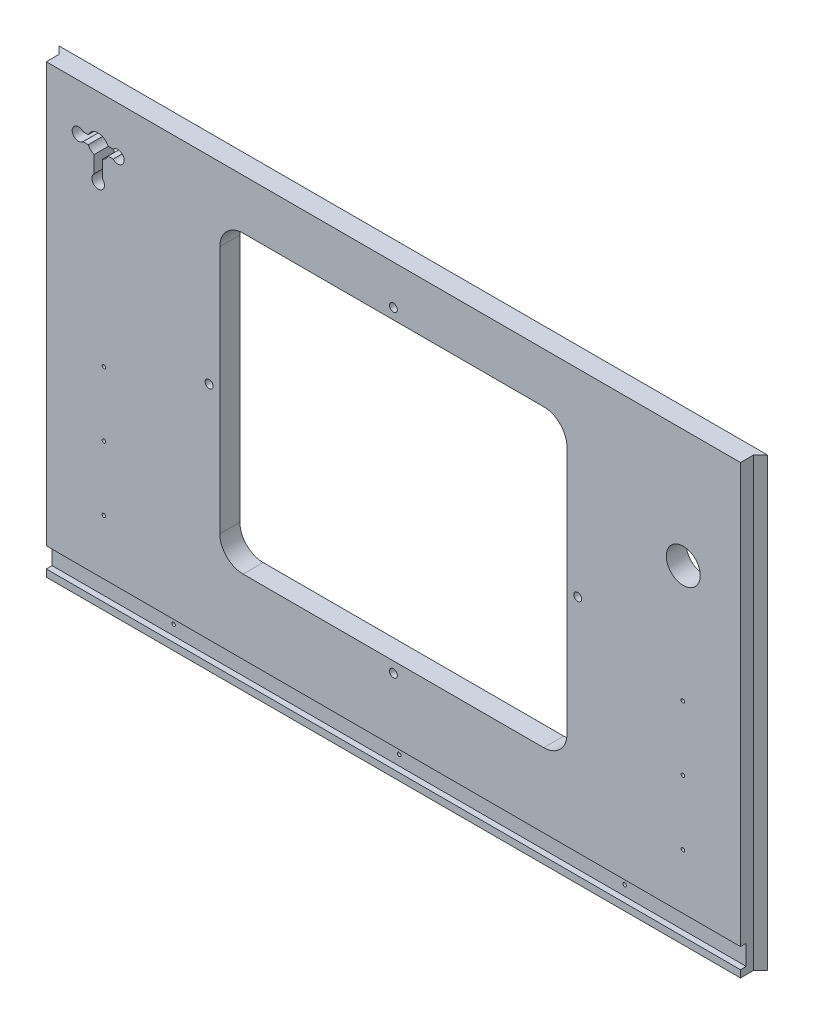
SolidWorks part; units mm, degrees
material "Pine"
ref_plane "Front Plane" through (0, 0, 0) normal (0, 0, 1) x (1, 0, 0)
ref_plane "Top Plane" through (0, 0, 0) normal (0, 1, 0) x (1, 0, 0)
ref_plane "Right Plane" through (0, 0, 0) normal (1, 0, 0) x (0, 0, -1)
sketch "Sketch1" plane through (0, 0, 0) normal (0, 0, 1) x (1, 0, 0)
  line L0 (8932.6508, -5243.5125) -> (10226.1458, -5243.5125)
  line L1 (9086.3208, -4722.0918) -> (10222.9708, -4853.7812)
  line L2 (8914.8708, -6342.0625) -> (10197.5708, -6342.0625)
  line L3 (8914.8708, -5808.6625) -> (10197.5708, -5808.6625)
  line L4 (8919.6333, -5253.0375) -> (10218.2083, -5253.0375)
  line L5 (9134.2633, -4656.1375) -> (9134.2633, -4638.3575)
  line L6 (9091.0833, -4638.3575) -> (9134.2633, -4638.3575)
  line L7 (9091.0833, -4567.2375) -> (9091.0833, -4638.3575)
  line L8 (9134.2633, -4656.1375) -> (9581.3033, -4656.1375)
  line L9 (9091.0833, -4567.2375) -> (9624.4833, -4567.2375)
  line L10 (9581.3033, -4656.1375) -> (9581.3033, -4638.3575)
  line L11 (9581.3033, -4638.3575) -> (9624.4833, -4638.3575)
  line L12 (9624.4833, -4567.2375) -> (9624.4833, -4638.3575)
  line L13 (8932.6508, -5225.7325) -> (9344.9775, -5225.7325)
  line L14 (8932.6508, -5256.2125) -> (8932.6508, -5243.5125)
  line L15 (8911.6958, -5256.2125) -> (8932.6508, -5256.2125)
  line L16 (8914.8708, -4722.0918) -> (9086.3208, -4722.0918)
  line L17 (8911.6958, -4715.5913) -> (8932.6508, -4715.5913)
  line L18 (8914.8708, -6342.0625) -> (8914.8708, -5808.6625)
  line L19 (12082.9917, -4722.0918) -> (10946.3417, -4853.7812)
  line L20 (12236.6617, -5243.5125) -> (10943.1667, -5243.5125)
  line L21 (10951.1042, -5253.0375) -> (12249.6792, -5253.0375)
  line L22 (10838.3917, -5656.2625) -> (11308.2917, -5656.2625)
  line L23 (10838.3917, -5719.7625) -> (11308.2917, -5719.7625)
  line L24 (10838.3917, -5742.5368) -> (11308.2917, -5742.5368)
  line L25 (10806.6417, -6342.0625) -> (11340.0417, -6342.0625)
  line L26 (10803.4667, -6335.7125) -> (11343.2167, -6335.7125)
  line L27 (10803.4667, -6317.9325) -> (11343.2167, -6317.9325)
  line L28 (10943.1667, -5225.7325) -> (11376.4483, -5225.7325)
  line L29 (11506.7292, -4754.5625) -> (10806.6417, -4827.5875)
  line L30 (11506.7292, -4567.2375) -> (11506.7292, -4754.5625)
  line L31 (10806.6417, -4567.2375) -> (10806.6417, -4827.5875)
  line L32 (10806.6417, -4567.2375) -> (11506.7292, -4567.2375)
  line L33 (10235.6708, -6329.3625) -> (10245.1958, -6329.3625)
  line L34 (10245.1958, -6329.3625) -> (10254.7208, -6278.5625)
  line L35 (10302.3458, -6329.3625) -> (10311.8708, -6278.5625)
  line L36 (10302.3458, -6329.3625) -> (10292.8208, -6329.3625)
  line L37 (10245.1958, -5821.3625) -> (10254.7208, -5872.1625)
  line L38 (10235.6708, -5821.3625) -> (10245.1958, -5821.3625)
  line L39 (10292.8208, -5821.3625) -> (10302.3458, -5821.3625)
  line L40 (10302.3458, -5821.3625) -> (10311.8708, -5872.1625)
  line L41 (10235.6708, -5821.3625) -> (10235.6708, -6329.3625)
  line L42 (10254.7208, -5872.1625) -> (10254.7208, -6278.5625)
  line L43 (10311.8708, -5872.1625) -> (10311.8708, -6278.5625)
  line L44 (10292.8208, -5821.3625) -> (10292.8208, -6329.3625)
  line L45 (8932.6508, -5225.7325) -> (8932.6508, -4715.5913)
  line L46 (8911.6958, -4715.5913) -> (8911.6958, -5256.2125)
  line L47 (8914.8708, -5248.275) -> (8914.8708, -4722.0918)
  line L48 (8919.6333, -5253.0375) -> (8914.8708, -5248.275)
  line L49 (8914.8708, -5145.0875) -> (8937.426, -5145.0875)
  line L50 (8914.8708, -5202.2375) -> (8937.426, -5202.2375)
  line L51 (10838.3917, -5656.2625) -> (10838.3917, -5719.7625)
  line L52 (10832.0417, -5736.1868) -> (10856.1717, -5736.1868)
  line L53 (10806.6417, -6342.0625) -> (10806.6417, -5818.7368)
  line L54 (10832.0417, -5649.9125) -> (10856.1717, -5649.9125)
  line L55 (10832.0417, -5726.1125) -> (10856.1717, -5726.1125)
  line L56 (10806.6417, -5818.7368) -> (10833.9015, -5818.7368)
  line L57 (10832.0417, -5806.0442) -> (10851.6815, -5806.0442)
  line L58 (10856.1717, -5801.5541) -> (10856.1717, -5736.1868)
  line L59 (10838.3917, -5814.2467) -> (10838.3917, -5742.5368)
  line L60 (10832.0417, -5806.0442) -> (10832.0417, -5736.1868)
  line L61 (10803.4667, -6317.9325) -> (10803.4667, -6335.7125)
  line L62 (10197.5708, -5808.6625) -> (10197.5708, -6342.0625)
  line L63 (9762.3842, -6348.4125) -> (9762.3842, -5802.3125)
  line L64 (9780.1642, -6348.4125) -> (9762.3842, -6348.4125)
  line L65 (9780.1642, -5802.3125) -> (9780.1642, -6348.4125)
  line L66 (9762.3842, -5802.3125) -> (9780.1642, -5802.3125)
  line L67 (9332.2775, -6348.4125) -> (9332.2775, -5802.3125)
  line L68 (9332.2775, -6348.4125) -> (9350.0575, -6348.4125)
  line L69 (9350.0575, -5802.3125) -> (9350.0575, -6348.4125)
  line L70 (9332.2775, -5802.3125) -> (9350.0575, -5802.3125)
  line L71 (9993.8374, -6061.075) -> (9993.8374, -6045.2418)
  line L72 (9998.5999, -6065.8375) -> (10014.4331, -6065.8375)
  line L73 (9998.5999, -6084.8875) -> (10014.4331, -6084.8875)
  line L74 (9993.8374, -6105.4832) -> (9993.8374, -6089.65)
  line L75 (9974.7874, -6105.4832) -> (9974.7874, -6089.65)
  line L76 (9954.1917, -6084.8875) -> (9970.0249, -6084.8875)
  line L77 (9974.7874, -6061.075) -> (9974.7874, -6045.2418)
  line L78 (9954.1917, -6065.8375) -> (9970.0249, -6065.8375)
  line L79 (10793.9417, -6237.2875) -> (10816.4969, -6237.2875)
  line L80 (10793.9417, -6294.4375) -> (10816.4969, -6294.4375)
  line L81 (10856.1717, -5649.9125) -> (10856.1717, -5726.1125)
  line L82 (10832.0417, -5726.1125) -> (10832.0417, -5649.9125)
  line L83 (10226.1458, -5225.7325) -> (10226.1458, -5243.5125)
  line L84 (10205.1908, -5257.8) -> (10205.1908, -4844.2499)
  line L85 (10230.9083, -4844.2499) -> (10230.9083, -5257.8)
  line L86 (10205.1908, -5257.8) -> (10230.9083, -5257.8)
  line L87 (10205.1908, -4844.2499) -> (10230.9083, -4844.2499)
  line L88 (10946.3417, -5176.8375) -> (10968.8969, -5176.8375)
  line L89 (9349.4676, -5141.9125) -> (9358.2674, -5141.9125)
  line L90 (10946.3417, -5119.6875) -> (10968.8969, -5119.6875)
  line L91 (9929.011, -4660.9635) -> (10066.0807, -4660.9635)
  line L92 (9929.011, -4678.7435) -> (10066.0807, -4678.7435)
  line L93 (10943.1667, -5225.7325) -> (10943.1667, -5243.5125)
  line L94 (10946.3417, -5248.275) -> (10951.1042, -5253.0375)
  line L95 (10946.3417, -5257.8063) -> (10946.3417, -4849.0188)
  line L96 (10964.1217, -5257.8) -> (10964.1217, -4844.2499)
  line L97 (10938.4042, -4844.2499) -> (10938.4042, -5257.8)
  line L98 (10938.4042, -5257.8) -> (10964.1217, -5257.8)
  line L99 (10964.1217, -4844.2499) -> (10938.4042, -4844.2499)
  line L100 (10344.8908, -4560.8875) -> (10369.0208, -4560.8875)
  line L101 (10344.8908, -4560.8875) -> (10369.0208, -4560.8875)
  line L102 (10800.2917, -4560.8875) -> (10824.4217, -4560.8875)
  line L103 (10200.4156, -5119.6875) -> (10222.9708, -5119.6875)
  line L104 (10200.4156, -5176.8375) -> (10222.9708, -5176.8375)
  line L105 (9344.9775, -5146.4026) -> (9344.9775, -5225.7325)
  line L106 (10344.8908, -4560.8875) -> (10344.8908, -4833.9375)
  line L107 (9792.8642, -5225.7325) -> (9792.8642, -5146.4026)
  line L108 (9362.7575, -5225.7325) -> (9775.0842, -5225.7325)
  line L109 (9680.3633, -4761.8396) -> (9680.3633, -4559.9604)
  line L110 (9656.2333, -4559.9604) -> (9680.3633, -4559.9604)
  line L111 (9656.2333, -4761.8396) -> (9680.3633, -4761.8396)
  line L112 (9656.2333, -4761.8396) -> (9656.2333, -4559.9604)
  line L113 (9779.5743, -5141.9125) -> (9788.374, -5141.9125)
  line L114 (10070.5708, -4665.4536) -> (10070.5708, -4674.2534)
  line L115 (9924.5208, -4674.2534) -> (9924.5208, -4665.4536)
  line L116 (12127.4417, -6188.3925) -> (12205.5015, -6188.3925)
  line L117 (12209.9917, -6170.6125) -> (12209.9917, -6183.9024)
  line L118 (9792.8642, -5225.7325) -> (10226.1458, -5225.7325)
  line L119 (9662.5833, -4754.5625) -> (10362.6708, -4827.5875)
  line L120 (9662.5833, -4567.2375) -> (9662.5833, -4754.5625)
  line L121 (10362.6708, -4567.2375) -> (10362.6708, -4827.5875)
  line L122 (9662.5833, -4567.2375) -> (10362.6708, -4567.2375)
  line L123 (10824.4217, -4833.9375) -> (10800.2917, -4833.9375)
  line L124 (10800.2917, -4833.9375) -> (10800.2917, -4560.8875)
  line L125 (10824.4217, -4560.8875) -> (10824.4217, -4833.9375)
  line L126 (10344.8908, -4833.9375) -> (10369.0208, -4833.9375)
  line L127 (10369.0208, -4833.9375) -> (10369.0208, -4560.8875)
  line L128 (10222.9708, -5248.275) -> (10218.2083, -5253.0375)
  line L129 (10222.9708, -5257.8063) -> (10222.9708, -4849.0188)
  line L130 (11734.6544, -5701.375) -> (11739.2301, -5701.375)
  line L131 (9362.7575, -5225.7325) -> (9362.7575, -5146.4026)
  line L132 (9775.0842, -5146.4026) -> (9775.0842, -5225.7325)
  line L133 (11761.3864, -5701.375) -> (11756.8282, -5701.375)
  line L134 (11734.6544, -5693.755) -> (11739.2301, -5693.755)
  line L135 (11761.4039, -5693.755) -> (11756.8282, -5693.755)
  line L136 (11734.6544, -5701.375) -> (11739.2301, -5701.375)
  line L137 (11744.3462, -5721.3024) -> (11744.3462, -5706.4179)
  line L138 (11751.7122, -5721.3024) -> (11751.7122, -5706.4179)
  line L139 (11740.0917, -6170.6125) -> (11740.0917, -6183.9024)
  line L140 (11689.2917, -6188.3925) -> (11822.6417, -6188.3925)
  line L141 (11689.2917, -6348.4093) -> (11689.2917, -6164.2657)
  line L142 (11689.2917, -6164.2657) -> (11746.4417, -6164.2657)
  line L143 (11746.4417, -6164.2657) -> (11746.4417, -6188.3925)
  line L144 (11689.2917, -6164.2657) -> (11746.4417, -6164.2657)
  line L145 (11340.0417, -5818.7368) -> (11340.0417, -6342.0625)
  line L146 (11290.5117, -5726.1125) -> (11314.6417, -5726.1125)
  line L147 (11290.5117, -5649.9125) -> (11290.5117, -5726.1125)
  line L148 (11340.0417, -5818.7368) -> (11312.7818, -5818.7368)
  line L149 (11314.6417, -5806.0442) -> (11295.0018, -5806.0442)
  line L150 (11290.5117, -5801.5541) -> (11290.5117, -5736.1868)
  line L151 (11308.2917, -5814.2467) -> (11308.2917, -5742.5368)
  line L152 (11314.6417, -5806.0442) -> (11314.6417, -5736.1868)
  line L153 (11290.5117, -5736.1868) -> (11314.6417, -5736.1868)
  line L154 (11848.0417, -6267.1325) -> (11962.3417, -6267.1325)
  line L155 (11962.3417, -6267.1325) -> (11962.3417, -6203.6325)
  line L156 (11343.2167, -6317.9325) -> (11343.2167, -6335.7125)
  line L157 (11365.4417, -5656.2625) -> (11365.4417, -5719.7625)
  line L158 (11365.4417, -5656.2625) -> (11479.7417, -5656.2625)
  line L159 (11778.1917, -6071.3937) -> (11802.3217, -6071.3937)
  line L160 (11314.6417, -5726.1125) -> (11314.6417, -5649.9125)
  line L161 (11314.6417, -5649.9125) -> (11290.5117, -5649.9125)
  line L162 (11308.2917, -5719.7625) -> (11308.2917, -5656.2625)
  line L163 (11689.2917, -6348.4093) -> (11713.4217, -6348.4093)
  line L164 (12203.6417, -6164.2657) -> (12260.7917, -6164.2657)
  line L165 (11713.4217, -6348.4093) -> (11713.4217, -6164.2657)
  line L166 (11695.6417, -6342.0625) -> (11695.6417, -6170.6125)
  line L167 (11695.6417, -6048.5337) -> (11699.4517, -6052.3437)
  line L168 (11822.6417, -6292.5325) -> (11822.6417, -6188.3925)
  line L169 (11695.6417, -6342.0625) -> (11695.6417, -6170.6125)
  line L170 (11848.0417, -6203.6325) -> (11962.3417, -6203.6325)
  line L171 (11848.0417, -6203.6325) -> (11848.0417, -6267.1325)
  line L172 (11987.7417, -6267.1325) -> (11987.7417, -6203.6325)
  line L173 (11784.5417, -6077.7437) -> (11784.5417, -6141.2438)
  line L174 (11517.8417, -5656.2625) -> (11632.1417, -5656.2625)
  line L175 (11632.1417, -5656.2625) -> (11632.1417, -5719.7625)
  line L176 (11632.1417, -5719.7625) -> (11517.8417, -5719.7625)
  line L177 (11517.8417, -5719.7625) -> (11517.8417, -5656.2625)
  line L178 (11692.4667, -6028.2137) -> (11692.4667, -6045.9937)
  line L179 (11695.6417, -5979.3188) -> (11718.1969, -5979.3188)
  line L180 (11695.6417, -5922.1687) -> (11718.1969, -5922.1687)
  line L181 (11821.0415, -5722.9375) -> (11821.0415, -5943.6)
  line L182 (11687.7042, -5651.5) -> (11701.9917, -5651.5)
  line L183 (11687.7042, -5651.5) -> (11687.7042, -6055.5251)
  line L184 (11687.7042, -6055.5251) -> (11701.9917, -6055.5251)
  line L185 (11701.9917, -6055.5251) -> (11701.9917, -5651.5)
  line L186 (11695.6417, -6055.2013) -> (11695.6417, -5649.595)
  line L187 (11695.6417, -5656.2625) -> (11695.6417, -6048.5337)
  line L188 (11695.6417, -6170.6125) -> (11740.0917, -6170.6125)
  line L189 (12203.6417, -6164.2657) -> (12203.6417, -6188.3925)
  line L190 (12254.4417, -6342.0625) -> (12254.4417, -6170.6125)
  line L191 (12129.0419, -5943.6) -> (12129.0419, -5722.9375)
  line L192 (12254.4417, -6048.5337) -> (12250.6317, -6052.3437)
  line L193 (12257.6167, -6045.9937) -> (12257.6167, -6028.2137)
  line L194 (12248.0917, -5651.5) -> (12262.3792, -5651.5)
  line L195 (12262.3792, -5651.5) -> (12262.3792, -6055.5251)
  line L196 (12262.3792, -6055.5251) -> (12248.0917, -6055.5251)
  line L197 (12248.0917, -6055.5251) -> (12248.0917, -5651.5)
  line L198 (12254.4417, -6141.2438) -> (12254.4417, -6077.7437)
  line L199 (12236.6617, -6164.2657) -> (12260.7917, -6164.2657)
  line L200 (12102.0417, -6267.1325) -> (11987.7417, -6267.1325)
  line L201 (11330.1865, -6237.2875) -> (11352.7417, -6237.2875)
  line L202 (11330.1865, -6294.4375) -> (11352.7417, -6294.4375)
  line L203 (11474.6617, -5851.8425) -> (11492.4417, -5851.8425)
  line L204 (11474.6617, -5808.6625) -> (11474.6617, -5851.8425)
  line L205 (11403.5417, -5808.6625) -> (11474.6617, -5808.6625)
  line L206 (11492.4417, -5851.8425) -> (11492.4417, -6298.8825)
  line L207 (11403.5417, -6342.0625) -> (11403.5417, -5808.6625)
  line L208 (11474.6617, -6298.8825) -> (11492.4417, -6298.8825)
  line L209 (11474.6617, -6342.0625) -> (11474.6617, -6298.8825)
  line L210 (11403.5417, -6342.0625) -> (11474.6617, -6342.0625)
  line L211 (11619.4417, -5851.8425) -> (11601.6617, -5851.8425)
  line L212 (11601.6617, -5808.6625) -> (11601.6617, -5851.8425)
  line L213 (11530.5417, -5808.6625) -> (11601.6617, -5808.6625)
  line L214 (11619.4417, -5851.8425) -> (11619.4417, -6298.8825)
  line L215 (11530.5417, -6342.0625) -> (11530.5417, -5808.6625)
  line L216 (11619.4417, -6298.8825) -> (11601.6617, -6298.8825)
  line L217 (11601.6617, -6342.0625) -> (11601.6617, -6298.8825)
  line L218 (11530.5417, -6342.0625) -> (11601.6617, -6342.0625)
  line L219 (11479.7417, -5719.7625) -> (11479.7417, -5656.2625)
  line L220 (11365.4417, -5719.7625) -> (11479.7417, -5719.7625)
  line L221 (11778.1917, -6147.5937) -> (11802.3217, -6147.5937)
  line L222 (11802.3217, -6071.3937) -> (11802.3217, -6147.5937)
  line L223 (11778.1917, -6147.5937) -> (11778.1917, -6071.3937)
  line L224 (12254.4417, -5922.1687) -> (12231.8865, -5922.1687)
  line L225 (12254.4417, -5979.3188) -> (12231.8865, -5979.3188)
  line L226 (12254.4417, -6055.2013) -> (12254.4417, -5649.595)
  line L227 (12254.4417, -6048.5337) -> (12254.4417, -5656.2625)
  line L228 (11841.6917, -5702.2873) -> (12108.3917, -5702.2873)
  line L229 (11822.6417, -6292.5325) -> (12127.4417, -6292.5325)
  line L230 (12127.4417, -6292.5325) -> (12127.4417, -6188.3925)
  line L231 (12254.4417, -6170.6125) -> (12209.9917, -6170.6125)
  line L232 (11695.6417, -6342.0625) -> (12254.4417, -6342.0625)
  line L233 (12236.6617, -6348.4093) -> (12260.7917, -6348.4093)
  line L234 (12260.7917, -6348.4093) -> (12260.7917, -6164.2657)
  line L235 (12236.6617, -6348.4093) -> (12236.6617, -6164.2657)
  line L236 (12102.0417, -6203.6325) -> (12102.0417, -6267.1325)
  line L237 (11987.7417, -6203.6325) -> (12102.0417, -6203.6325)
  line L238 (12236.6617, -6147.5937) -> (12236.6617, -6071.3937)
  line L239 (12203.6417, -6188.3925) -> (12260.7917, -6188.3925)
  line L240 (11098.7417, -4665.4536) -> (11098.7417, -4674.2534)
  line L241 (11394.2283, -5146.4026) -> (11394.2283, -5225.7325)
  line L242 (11376.4483, -5225.7325) -> (11376.4483, -5146.4026)
  line L243 (11394.2283, -5225.7325) -> (11806.555, -5225.7325)
  line L244 (11841.6917, -5964.2502) -> (12108.3917, -5964.2502)
  line L245 (12236.6617, -6147.5937) -> (12260.7917, -6147.5937)
  line L246 (12236.6617, -5256.2125) -> (12236.6617, -5243.5125)
  line L247 (12260.7917, -6147.5937) -> (12260.7917, -6071.3937)
  line L248 (12260.7917, -6071.3937) -> (12236.6617, -6071.3937)
  line L249 (12254.4417, -6077.7437) -> (11784.5417, -6077.7437)
  line L250 (11784.5417, -6141.2438) -> (12254.4417, -6141.2438)
  line L252 (12254.4417, -5656.2625) -> (11695.6417, -5656.2625)
  line L253 (11699.4517, -6052.3437) -> (12250.6317, -6052.3437)
  line L254 (11692.4667, -6045.9937) -> (12257.6167, -6045.9937)
  line L255 (11692.4667, -6028.2137) -> (12257.6167, -6028.2137)
  line L256 (11824.335, -5146.4026) -> (11824.335, -5225.7325)
  line L257 (11811.0451, -5141.9125) -> (11819.8449, -5141.9125)
  line L258 (11244.7917, -4674.2534) -> (11244.7917, -4665.4536)
  line L259 (11806.555, -5225.7325) -> (11806.555, -5146.4026)
  line L260 (11488.9492, -4761.8396) -> (11488.9492, -4559.9604)
  line L261 (11488.9492, -4559.9604) -> (11513.0792, -4559.9604)
  line L262 (11488.9492, -4761.8396) -> (11513.0792, -4761.8396)
  line L263 (11513.0792, -4761.8396) -> (11513.0792, -4559.9604)
  line L264 (11240.3015, -4660.9635) -> (11103.2318, -4660.9635)
  line L265 (11103.2318, -4678.7435) -> (11240.3015, -4678.7435)
  line L266 (12236.6617, -5225.7325) -> (12236.6617, -4715.5913)
  line L267 (12257.6167, -4715.5913) -> (12257.6167, -5256.2125)
  line L268 (12254.4417, -5248.275) -> (12254.4417, -4722.0918)
  line L269 (12236.6617, -5225.7325) -> (11824.335, -5225.7325)
  line L270 (12035.0492, -4656.1375) -> (12035.0492, -4638.3575)
  line L271 (12078.2292, -4638.3575) -> (12035.0492, -4638.3575)
  line L272 (12078.2292, -4567.2375) -> (12078.2292, -4638.3575)
  line L273 (12035.0492, -4656.1375) -> (11588.0092, -4656.1375)
  line L274 (11544.8292, -4567.2375) -> (12078.2292, -4567.2375)
  line L275 (11588.0092, -4656.1375) -> (11588.0092, -4638.3575)
  line L276 (11544.8292, -4638.3575) -> (11588.0092, -4638.3575)
  line L277 (11544.8292, -4567.2375) -> (11544.8292, -4638.3575)
  line L278 (12249.6792, -5253.0375) -> (12254.4417, -5248.275)
  line L280 (12257.6167, -5256.2125) -> (12236.6617, -5256.2125)
  line L281 (12231.8865, -5145.0875) -> (12254.4417, -5145.0875)
  line L282 (12231.8865, -5202.2375) -> (12254.4417, -5202.2375)
  line L283 (12236.6617, -4715.5913) -> (12257.6167, -4715.5913)
  line L284 (12082.9917, -4722.0918) -> (12254.4417, -4722.0918)
  line L285 (11380.9385, -5141.9125) -> (11389.7382, -5141.9125)
  circle A0 centre (8923.7608, -4778.9042) radius 1.5875
  circle A1 centre (9062.6598, -4736.3765) radius 2.3685
  circle A2 centre (9051.3958, -6281.7375) radius 22.225
  circle A3 centre (9083.1458, -6249.9875) radius 1.5875
  circle A4 centre (9083.1458, -6313.4875) radius 1.5875
  circle A5 centre (9019.6458, -6249.9875) radius 1.5875
  circle A6 centre (9019.6458, -6313.4875) radius 1.5875
  circle A7 centre (8972.3383, -5202.2375) radius 1.5875
  circle A8 centre (8923.7608, -5015.9708) radius 1.5875
  circle A9 centre (8923.7608, -5134.5042) radius 1.5875
  circle A10 centre (9054.5708, -5234.6225) radius 1.5875
  circle A11 centre (8923.7608, -4897.4375) radius 1.5875
  circle A12 centre (8972.3383, -5087.9375) radius 1.5875
  circle A13 centre (8972.3383, -5145.0875) radius 1.5875
  circle A14 centre (10847.2817, -5668.9625) radius 1.5875
  circle A15 centre (10847.2817, -5707.0625) radius 1.5875
  circle A16 centre (10847.2817, -5755.2368) radius 1.5875
  circle A17 centre (10851.4092, -6237.2875) radius 1.5875
  circle A18 centre (10851.4092, -6294.4375) radius 1.5875
  circle A19 centre (10847.2817, -5793.3442) radius 1.5875
  arc A20 (10833.9015, -5818.7368) -> (10838.3917, -5814.2467) centre (10836.1466, -5816.4918) ccw
  arc A21 (10851.6815, -5806.0442) -> (10856.1717, -5801.5541) centre (10853.9266, -5803.7992) ccw
  circle A22 centre (10882.8417, -6040.4375) radius 1.5875
  circle A23 centre (10882.8417, -6218.2375) radius 1.5875
  circle A24 centre (10882.8417, -5862.6375) radius 1.5875
  circle A25 centre (10908.2417, -6326.8225) radius 1.5875
  circle A26 centre (10908.2417, -6326.8225) radius 1.5875
  circle A27 centre (10851.4092, -6180.1375) radius 1.5875
  circle A28 centre (10815.5317, -4783.4231) radius 1.5875
  circle A29 centre (10815.5317, -4696.9488) radius 1.5875
  circle A30 centre (10815.5317, -4610.4746) radius 1.5875
  circle A31 centre (10979.1323, -4867.0082) radius 2.3685
  circle A32 centre (10190.1802, -4867.0082) radius 2.3685
  circle A33 centre (10955.2317, -4929.9812) radius 1.5875
  circle A34 centre (10955.2317, -5031.5812) radius 1.5875
  circle A35 centre (10214.0808, -4929.9812) radius 1.5875
  circle A36 centre (10214.0808, -5031.5812) radius 1.5875
  circle A37 centre (9341.1675, -6265.8625) radius 1.5875
  circle A38 centre (9771.2742, -5884.8625) radius 1.5875
  circle A39 centre (9771.2742, -6138.8625) radius 1.5875
  circle A40 centre (9771.2742, -6011.8625) radius 1.5875
  arc A41 (10036.2287, -6113.8083) -> (10051.3426, -6111.6033) centre (10042.9639, -6107.0732) ccw
  arc A42 (10051.3426, -6111.6033) -> (10051.3426, -6039.1217) centre (9984.3124, -6075.3625) ccw
  arc A43 (10051.3426, -6039.1217) -> (10036.2287, -6036.9167) centre (10042.9639, -6043.6518) ccw
  arc A44 (10034.5851, -6102.5431) -> (10034.5851, -6048.1819) centre (9984.3124, -6075.3625) ccw
  arc A45 (10034.5851, -6102.5431) -> (10036.2287, -6113.8083) centre (10042.9639, -6107.0732) ccw
  arc A46 (10036.2287, -6036.9167) -> (10034.5851, -6048.1819) centre (10042.9639, -6043.6518) ccw
  arc A47 (9945.8666, -6127.2787) -> (9948.0717, -6142.3927) centre (9952.6018, -6134.0139) ccw
  arc A48 (9948.0717, -6142.3927) -> (10020.5532, -6142.3927) centre (9984.3124, -6075.3625) ccw
  arc A49 (10020.5532, -6142.3927) -> (10022.7583, -6127.2787) centre (10016.0231, -6134.0139) ccw
  arc A50 (9957.1319, -6125.6352) -> (10011.493, -6125.6352) centre (9984.3124, -6075.3625) ccw
  arc A51 (9957.1319, -6125.6352) -> (9945.8666, -6127.2787) centre (9952.6018, -6134.0139) ccw
  arc A52 (10022.7583, -6127.2787) -> (10011.493, -6125.6352) centre (10016.0231, -6134.0139) ccw
  arc A53 (9932.3962, -6036.9167) -> (9917.2822, -6039.1217) centre (9925.661, -6043.6518) ccw
  arc A54 (9917.2822, -6039.1217) -> (9917.2822, -6111.6033) centre (9984.3124, -6075.3625) ccw
  arc A55 (9917.2822, -6111.6033) -> (9932.3962, -6113.8083) centre (9925.661, -6107.0732) ccw
  arc A56 (9934.0398, -6048.1819) -> (9934.0398, -6102.5431) centre (9984.3124, -6075.3625) ccw
  arc A57 (9934.0398, -6048.1819) -> (9932.3962, -6036.9167) centre (9925.661, -6043.6518) ccw
  arc A58 (9932.3962, -6113.8083) -> (9934.0398, -6102.5431) centre (9925.661, -6107.0732) ccw
  arc A59 (9945.8666, -6023.4463) -> (9957.1319, -6025.0898) centre (9952.6018, -6016.7111) ccw
  arc A60 (10011.493, -6025.0898) -> (10022.7583, -6023.4463) centre (10016.0231, -6016.7111) ccw
  arc A61 (10011.493, -6025.0898) -> (9957.1319, -6025.0898) centre (9984.3124, -6075.3625) ccw
  arc A62 (9948.0717, -6008.3323) -> (9945.8666, -6023.4463) centre (9952.6018, -6016.7111) ccw
  arc A63 (10020.5532, -6008.3323) -> (9948.0717, -6008.3323) centre (9984.3124, -6075.3625) ccw
  arc A64 (10022.7583, -6023.4463) -> (10020.5532, -6008.3323) centre (10016.0231, -6016.7111) ccw
  arc A65 (10005.0943, -6187.7574) -> (10096.7073, -6096.1443) centre (9984.3124, -6075.3625) ccw
  arc A66 (9993.8374, -6178.3911) -> (10005.0943, -6187.7574) centre (10003.3624, -6178.3911) ccw
  arc A67 (10001.6306, -6169.0249) -> (10077.9748, -6092.6807) centre (9984.3124, -6075.3625) ccw
  arc A68 (10087.3411, -6084.8875) -> (10077.9748, -6092.6807) centre (10087.3411, -6094.4125) ccw
  arc A69 (10001.6306, -6169.0249) -> (9993.8374, -6178.3911) centre (10003.3624, -6178.3911) ccw
  arc A70 (9963.5306, -6187.7574) -> (9974.7874, -6178.3911) centre (9965.2624, -6178.3911) ccw
  arc A71 (9871.9176, -6096.1443) -> (9963.5306, -6187.7574) centre (9984.3124, -6075.3625) ccw
  arc A72 (9881.2838, -6084.8875) -> (9871.9176, -6096.1443) centre (9881.2838, -6094.4125) ccw
  arc A73 (9890.65, -6092.6807) -> (9966.9943, -6169.0249) centre (9984.3124, -6075.3625) ccw
  arc A74 (9974.7874, -6178.3911) -> (9966.9943, -6169.0249) centre (9965.2624, -6178.3911) ccw
  arc A75 (9890.65, -6092.6807) -> (9881.2838, -6084.8875) centre (9881.2838, -6094.4125) ccw
  arc A76 (9871.9176, -6054.5807) -> (9881.2838, -6065.8375) centre (9881.2838, -6056.3125) ccw
  arc A77 (9963.5306, -5962.9676) -> (9871.9176, -6054.5807) centre (9984.3124, -6075.3625) ccw
  arc A78 (9974.7874, -5972.3339) -> (9963.5306, -5962.9676) centre (9965.2624, -5972.3339) ccw
  arc A79 (9966.9943, -5981.7001) -> (9890.65, -6058.0443) centre (9984.3124, -6075.3625) ccw
  arc A80 (9881.2838, -6065.8375) -> (9890.65, -6058.0443) centre (9881.2838, -6056.3125) ccw
  arc A81 (9966.9943, -5981.7001) -> (9974.7874, -5972.3339) centre (9965.2624, -5972.3339) ccw
  arc A82 (10077.9748, -6058.0443) -> (10087.3411, -6065.8375) centre (10087.3411, -6056.3125) ccw
  arc A83 (9993.8374, -5972.3339) -> (10001.6306, -5981.7001) centre (10003.3624, -5972.3339) ccw
  arc A84 (10077.9748, -6058.0443) -> (10001.6306, -5981.7001) centre (9984.3124, -6075.3625) ccw
  arc A85 (10087.3411, -6065.8375) -> (10096.7073, -6054.5807) centre (10087.3411, -6056.3125) ccw
  arc A86 (10096.7073, -6054.5807) -> (10005.0943, -5962.9676) centre (9984.3124, -6075.3625) ccw
  arc A87 (10005.0943, -5962.9676) -> (9993.8374, -5972.3339) centre (10003.3624, -5972.3339) ccw
  arc A88 (10014.4331, -6065.8375) -> (10018.7361, -6059.0339) centre (10014.4331, -6061.075) ccw
  arc A89 (10018.7361, -6059.0339) -> (10000.641, -6040.9388) centre (9984.3124, -6075.3625) ccw
  arc A90 (10000.641, -6040.9388) -> (9993.8374, -6045.2418) centre (9998.5999, -6045.2418) ccw
  arc A91 (9993.8374, -6061.075) -> (9998.5999, -6065.8375) centre (9998.5999, -6061.075) ccw
  arc A92 (9993.8374, -6105.4832) -> (10000.641, -6109.7862) centre (9998.5999, -6105.4832) ccw
  arc A93 (10000.641, -6109.7862) -> (10018.7361, -6091.6911) centre (9984.3124, -6075.3625) ccw
  arc A94 (10018.7361, -6091.6911) -> (10014.4331, -6084.8875) centre (10014.4331, -6089.65) ccw
  arc A95 (9998.5999, -6084.8875) -> (9993.8374, -6089.65) centre (9998.5999, -6089.65) ccw
  arc A96 (9954.1917, -6084.8875) -> (9949.8888, -6091.6911) centre (9954.1917, -6089.65) ccw
  arc A97 (9949.8888, -6091.6911) -> (9967.9839, -6109.7862) centre (9984.3124, -6075.3625) ccw
  arc A98 (9967.9839, -6109.7862) -> (9974.7874, -6105.4832) centre (9970.0249, -6105.4832) ccw
  arc A99 (9974.7874, -6089.65) -> (9970.0249, -6084.8875) centre (9970.0249, -6089.65) ccw
  arc A100 (9970.0249, -6065.8375) -> (9974.7874, -6061.075) centre (9970.0249, -6061.075) ccw
  arc A101 (9949.8888, -6059.0339) -> (9954.1917, -6065.8375) centre (9954.1917, -6061.075) ccw
  arc A102 (9967.9839, -6040.9388) -> (9949.8888, -6059.0339) centre (9984.3124, -6075.3625) ccw
  arc A103 (9974.7874, -6045.2418) -> (9967.9839, -6040.9388) centre (9970.0249, -6045.2418) ccw
  arc A104 (10096.7073, -6096.1443) -> (10087.3411, -6084.8875) centre (10087.3411, -6094.4125) ccw
  circle A105 centre (9771.2742, -6265.8625) radius 1.5875
  circle A106 centre (9341.1675, -5884.8625) radius 1.5875
  circle A107 centre (9341.1675, -6138.8625) radius 1.5875
  circle A108 centre (9341.1675, -6011.8625) radius 1.5875
  circle A109 centre (11037.2315, -4887.5494) radius 15.0812
  arc A110 (9349.4676, -5141.9125) -> (9344.9775, -5146.4026) centre (9347.2226, -5144.1576) ccw
  arc A111 (9362.7575, -5146.4026) -> (9358.2674, -5141.9125) centre (9360.5124, -5144.1576) ccw
  circle A112 centre (9946.7458, -4669.8535) radius 1.5875
  arc A113 (9924.5208, -4674.2534) -> (9929.011, -4678.7435) centre (9926.7659, -4676.4984) ccw
  circle A114 centre (11003.8092, -5176.8375) radius 1.5875
  circle A115 centre (11003.8092, -5119.6875) radius 1.5875
  circle A116 centre (10353.7808, -4696.9488) radius 1.5875
  circle A117 centre (10353.7808, -4610.4746) radius 1.5875
  circle A118 centre (10353.7808, -4783.4231) radius 1.5875
  circle A119 centre (11003.8092, -5062.5375) radius 1.5875
  circle A120 centre (9353.8675, -5160.9625) radius 1.5875
  circle A121 centre (9638.7708, -5234.6225) radius 1.5875
  circle A122 centre (9671.4733, -4724.1144) radius 1.5875
  circle A123 centre (9671.4733, -4661.3637) radius 1.5875
  circle A124 centre (9671.4733, -4598.6129) radius 1.5875
  arc A125 (9792.8642, -5146.4026) -> (9788.374, -5141.9125) centre (9790.6191, -5144.1576) ccw
  arc A126 (9779.5743, -5141.9125) -> (9775.0842, -5146.4026) centre (9777.3292, -5144.1576) ccw
  circle A127 centre (10048.3458, -4669.8535) radius 1.5875
  arc A128 (10070.5708, -4665.4536) -> (10066.0807, -4660.9635) centre (10068.3258, -4663.2086) ccw
  arc A129 (10066.0807, -4678.7435) -> (10070.5708, -4674.2534) centre (10068.3258, -4676.4984) ccw
  circle A130 centre (9997.5458, -4669.8535) radius 1.5875
  arc A131 (9929.011, -4660.9635) -> (9924.5208, -4665.4536) centre (9926.7659, -4663.2086) ccw
  circle A132 centre (10132.081, -4887.5494) radius 15.0812
  circle A133 centre (10165.5033, -5176.8375) radius 1.5875
  circle A134 centre (10165.5033, -5119.6875) radius 1.5875
  circle A135 centre (9486.3708, -5234.6225) radius 1.5875
  circle A136 centre (10165.5033, -5062.5375) radius 1.5875
  circle A137 centre (9206.9708, -5234.6225) radius 1.5875
  circle A138 centre (10070.5708, -5234.6225) radius 1.5875
  circle A139 centre (9918.1708, -5234.6225) radius 1.5875
  circle A140 centre (9783.9742, -5160.9625) radius 1.5875
  circle A141 centre (9783.9742, -5193.9825) radius 1.5875
  circle A142 centre (9353.8675, -5193.9825) radius 1.5875
  circle A143 centre (11073.3417, -6326.8225) radius 1.5875
  circle A144 centre (11073.3417, -6326.8225) radius 1.5875
  circle A145 centre (11295.2742, -6180.1375) radius 1.5875
  circle A146 centre (11295.2742, -6294.4375) radius 1.5875
  circle A147 centre (11295.2742, -6237.2875) radius 1.5875
  circle A148 centre (11975.0417, -5692.775) radius 3.4925
  circle A149 centre (11263.8417, -5862.6375) radius 1.5875
  arc A150 (11739.2301, -5701.375) -> (11744.3462, -5706.4179) centre (11748.0292, -5697.565) ccw
  arc A151 (11751.7122, -5706.4179) -> (11756.8282, -5701.375) centre (11748.0292, -5697.565) ccw
  arc A152 (11744.3462, -5721.3024) -> (11751.7122, -5721.3024) centre (11748.0292, -5725.505) ccw
  arc A153 (11734.6544, -5693.755) -> (11724.9787, -5697.565) centre (11730.5667, -5697.565) ccw
  arc A154 (11756.8282, -5693.755) -> (11739.2301, -5693.755) centre (11748.0292, -5697.565) ccw
  arc A155 (11724.9787, -5697.565) -> (11734.6544, -5701.375) centre (11730.5667, -5697.565) ccw
  arc A156 (11761.3864, -5701.375) -> (11771.0797, -5697.565) centre (11765.4842, -5697.565) ccw
  arc A157 (11771.0797, -5697.565) -> (11761.4039, -5693.755) centre (11765.4917, -5697.565) ccw
  arc A158 (11740.0917, -6183.9024) -> (11744.5818, -6188.3925) centre (11742.3367, -6186.1474) ccw
  arc A159 (12205.5015, -6188.3925) -> (12209.9917, -6183.9024) centre (12207.7466, -6186.1474) ccw
  circle A160 centre (11299.4017, -5793.3442) radius 1.5875
  arc A161 (11308.2917, -5814.2467) -> (11312.7818, -5818.7368) centre (11310.5367, -5816.4918) ccw
  arc A162 (11290.5117, -5801.5541) -> (11295.0018, -5806.0442) centre (11292.7567, -5803.7992) ccw
  circle A163 centre (11704.5317, -6314.149) radius 1.5875
  circle A164 centre (11748.9817, -6208.7125) radius 1.5875
  circle A165 centre (11263.8417, -6218.2375) radius 1.5875
  circle A166 centre (11263.8417, -6040.4375) radius 1.5875
  circle A167 centre (11238.4417, -6326.8225) radius 1.5875
  circle A168 centre (11238.4417, -6326.8225) radius 1.5875
  circle A169 centre (11299.4017, -5668.9625) radius 1.5875
  circle A170 centre (11299.4017, -5707.0625) radius 1.5875
  circle A171 centre (11726.7567, -6179.5025) radius 1.5875
  circle A172 centre (11704.5317, -6199.3198) radius 1.5875
  circle A173 centre (11748.9817, -6272.2125) radius 1.5875
  circle A174 centre (11704.5317, -6256.7344) radius 1.5875
  circle A175 centre (11299.4017, -5755.2368) radius 1.5875
  circle A176 centre (11913.4467, -6301.4225) radius 1.5875
  circle A177 centre (11790.2567, -6301.4225) radius 1.5875
  circle A178 centre (11793.4317, -6128.5437) radius 1.5875
  circle A179 centre (11753.1092, -5865.0188) radius 1.5875
  circle A180 centre (11809.9417, -6037.1038) radius 1.5875
  circle A181 centre (11809.9417, -6037.1038) radius 1.5875
  circle A182 centre (11753.1092, -5922.1687) radius 1.5875
  circle A183 centre (11975.0417, -5973.7625) radius 3.4925
  circle A184 centre (11975.0417, -6037.1038) radius 1.5875
  circle A185 centre (11753.1092, -5979.3188) radius 1.5875
  circle A186 centre (11975.0417, -6037.1038) radius 1.5875
  arc A187 (11841.6917, -5702.2873) -> (11821.0415, -5722.9375) centre (11841.6917, -5722.9375) ccw
  circle A188 centre (11811.5292, -5833.2687) radius 3.4925
  arc A189 (11821.0415, -5943.6) -> (11841.6917, -5964.2502) centre (11841.6917, -5943.6) ccw
  circle A190 centre (12196.9742, -5865.0188) radius 1.5875
  arc A191 (12129.0419, -5722.9375) -> (12108.3917, -5702.2873) centre (12108.3917, -5722.9375) ccw
  circle A192 centre (12036.6367, -6301.4225) radius 1.5875
  circle A193 centre (12159.8267, -6301.4225) radius 1.5875
  circle A194 centre (12138.5542, -5833.2687) radius 3.4925
  circle A195 centre (12197.2917, -5761.0375) radius 15.0812
  circle A196 centre (11793.4317, -6090.4437) radius 1.5875
  circle A197 centre (12196.9742, -5922.1687) radius 1.5875
  arc A198 (12108.3917, -5964.2502) -> (12129.0419, -5943.6) centre (12108.3917, -5943.6) ccw
  circle A199 centre (12196.9742, -5979.3188) radius 1.5875
  circle A200 centre (12201.1017, -6272.2125) radius 1.5875
  circle A201 centre (12245.5517, -6314.149) radius 1.5875
  circle A202 centre (12245.5517, -6256.7344) radius 1.5875
  circle A203 centre (12201.1017, -6208.7125) radius 1.5875
  circle A204 centre (12223.3267, -6179.5025) radius 1.5875
  circle A205 centre (12245.5517, -6199.3198) radius 1.5875
  circle A206 centre (11171.7667, -4669.8535) radius 1.5875
  circle A207 centre (11222.5667, -4669.8535) radius 1.5875
  arc A208 (11240.3015, -4678.7435) -> (11244.7917, -4674.2534) centre (11242.5466, -4676.4984) ccw
  circle A209 centre (11385.3383, -5193.9825) radius 1.5875
  circle A210 centre (12106.6527, -4736.3765) radius 2.3685
  circle A211 centre (12140.1417, -6037.1038) radius 1.5875
  circle A212 centre (12140.1417, -6037.1038) radius 1.5875
  circle A213 centre (12245.5517, -6090.4437) radius 1.5875
  circle A214 centre (12245.5517, -6128.5437) radius 1.5875
  circle A215 centre (11385.3383, -5160.9625) radius 1.5875
  arc A216 (11824.335, -5146.4026) -> (11819.8449, -5141.9125) centre (11822.0899, -5144.1576) ccw
  arc A217 (11811.0451, -5141.9125) -> (11806.555, -5146.4026) centre (11808.8001, -5144.1576) ccw
  circle A218 centre (11815.445, -5193.9825) radius 1.5875
  circle A219 centre (11815.445, -5160.9625) radius 1.5875
  circle A220 centre (11530.5417, -5234.6225) radius 1.5875
  circle A221 centre (11962.3417, -5234.6225) radius 1.5875
  arc A222 (11244.7917, -4665.4536) -> (11240.3015, -4660.9635) centre (11242.5466, -4663.2086) ccw
  circle A223 centre (11682.9417, -5234.6225) radius 1.5875
  circle A224 centre (11497.8392, -4724.1144) radius 1.5875
  circle A225 centre (11497.8392, -4661.3637) radius 1.5875
  circle A226 centre (11497.8392, -4598.6129) radius 1.5875
  circle A227 centre (11120.9667, -4669.8535) radius 1.5875
  arc A228 (11103.2318, -4660.9635) -> (11098.7417, -4665.4536) centre (11100.9867, -4663.2086) ccw
  arc A229 (11098.7417, -4674.2534) -> (11103.2318, -4678.7435) centre (11100.9867, -4676.4984) ccw
  circle A230 centre (12196.9742, -5202.2375) radius 1.5875
  circle A231 centre (12245.5517, -5015.9708) radius 1.5875
  circle A232 centre (12245.5517, -5134.5042) radius 1.5875
  circle A233 centre (12114.7417, -5234.6225) radius 1.5875
  circle A234 centre (12245.5517, -4897.4375) radius 1.5875
  circle A235 centre (12245.5517, -4778.9042) radius 1.5875
  circle A236 centre (12196.9742, -5087.9375) radius 1.5875
  circle A237 centre (12196.9742, -5145.0875) radius 1.5875
  circle A238 centre (11098.7417, -5234.6225) radius 1.5875
  circle A239 centre (11251.1417, -5234.6225) radius 1.5875
  arc A240 (11380.9385, -5141.9125) -> (11376.4483, -5146.4026) centre (11378.6934, -5144.1576) ccw
  arc A241 (11394.2283, -5146.4026) -> (11389.7382, -5141.9125) centre (11391.9833, -5144.1576) ccw
sketch "Sketch2" plane through (0, 0, 0) normal (0, 0, 1) x (1, 0, 0)
  line L0 (11695.6417, -6055.2013) -> (11695.6417, -5649.595) construction
  line L1 (11695.6417, -6052.3437) -> (12324.2917, -6052.3437)
  line L3 (12324.2917, -6052.3437) -> (12324.2917, -5656.2625)
  line L4 (12324.2917, -5656.2625) -> (11695.6417, -5656.2625)
  line L5 (11695.6417, -5656.2625) -> (11695.6417, -6052.3437)
  point P1 (0, 0)
  point P2 (0, 0)
  dimension "D1" = 628.65
extrude "Extrude1" add sketch "Sketch2" against normal blind 17.78
sketch "Sketch3" plane through (0, 0, 0) normal (0, 0, 1) x (1, 0, 0)
  line L0 (11855.9665, -5700.6998) -> (12163.9669, -5700.6998)
  line L1 (12163.9669, -5700.6998) -> (12163.9669, -5962.6627)
  line L2 (12163.9669, -5962.6627) -> (11855.9665, -5962.6627)
  line L3 (11855.9665, -5962.6627) -> (11855.9665, -5700.6998)
  line L4 (11734.6544, -5693.755) -> (11739.2301, -5693.755)
  line L5 (11734.6544, -5701.375) -> (11739.2301, -5701.375)
  line L6 (11744.3462, -5706.4179) -> (11744.3462, -5721.3024)
  line L7 (11751.7122, -5706.4179) -> (11751.7122, -5721.3024)
  line L8 (11756.8282, -5701.375) -> (11761.3864, -5701.375)
  line L9 (11761.3864, -5693.755) -> (11756.8282, -5693.755)
  line L10 (11753.1092, -5865.0188) -> (11753.1092, -5922.1687) construction
  line L11 (11753.1092, -5922.1687) -> (11753.1092, -5979.3188) construction
  line L12 (11695.6417, -5656.2625) -> (11695.6417, -6052.3437) construction
  line L13 (12266.8242, -5865.0188) -> (12266.8242, -5922.1687) construction
  line L14 (12266.8242, -5922.1687) -> (12266.8242, -5979.3188) construction
  line L15 (12324.2917, -6052.3437) -> (12324.2917, -5656.2625) construction
  line L16 (11809.9417, -6037.1038) -> (12009.9667, -6037.1038) construction
  line L17 (12009.9667, -6037.1038) -> (12209.9917, -6037.1038) construction
  line L18 (12009.9667, -6037.1038) -> (12009.9667, -6052.3437) construction
  line L19 (11695.6417, -6052.3437) -> (12324.2917, -6052.3437) construction
  line L20 (12009.9667, -5691.1875) -> (12009.9667, -5700.6998) construction
  line L21 (11846.4542, -5831.6812) -> (11855.9665, -5831.6812) construction
  line L22 (12009.9667, -5972.175) -> (12009.9667, -5962.6627) construction
  line L23 (12173.4792, -5831.6812) -> (12163.9669, -5831.6812) construction
  line L24 (12009.9667, -5691.1875) -> (12009.9667, -5656.2625) construction
  line L25 (12324.2917, -5656.2625) -> (11695.6417, -5656.2625) construction
  arc A4 (11734.6544, -5693.755) -> (11734.6544, -5701.375) centre (11730.5667, -5697.565) ccw
  arc A5 (11724.9787, -5697.565) -> (11734.6544, -5701.375) centre (11730.5667, -5697.565) ccw construction
  arc A6 (11739.2301, -5693.755) -> (11756.8282, -5693.755) centre (11748.0292, -5697.565) cw
  arc A7 (11756.8282, -5693.755) -> (11739.2301, -5693.755) centre (11748.0292, -5697.565) ccw construction
  arc A8 (11744.3462, -5721.3024) -> (11751.7122, -5721.3024) centre (11748.0292, -5725.505) ccw
  arc A9 (11744.3462, -5721.3024) -> (11751.7122, -5721.3024) centre (11748.0292, -5725.505) ccw construction
  arc A10 (11739.2301, -5701.375) -> (11744.3462, -5706.4179) centre (11748.0292, -5697.565) ccw
  arc A11 (11739.2301, -5701.375) -> (11744.3462, -5706.4179) centre (11748.0292, -5697.565) ccw construction
  arc A12 (11751.7122, -5706.4179) -> (11756.8282, -5701.375) centre (11748.0292, -5697.565) ccw
  arc A13 (11751.7122, -5706.4179) -> (11756.8282, -5701.375) centre (11748.0292, -5697.565) ccw construction
  arc A14 (11761.3864, -5701.375) -> (11771.0797, -5697.565) centre (11765.4842, -5697.565) ccw
  arc A16 (11761.3864, -5701.375) -> (11771.0797, -5697.565) centre (11765.4842, -5697.565) ccw construction
  arc A17 (11771.0797, -5697.565) -> (11761.3864, -5693.755) centre (11765.4842, -5697.565) ccw
  circle A18 centre (12267.1417, -5761.0375) radius 15.0812
  circle A19 centre (12173.4792, -5831.6812) radius 3.4925
  circle A20 centre (12266.8242, -5865.0188) radius 1.5875
  circle A21 centre (12266.8242, -5922.1687) radius 1.5875
  circle A22 centre (12266.8242, -5979.3188) radius 1.5875
  circle A23 centre (12209.9917, -6037.1038) radius 1.5875
  circle A24 centre (12009.9667, -6037.1038) radius 1.5875
  circle A25 centre (11809.9417, -6037.1038) radius 1.5875
  circle A26 centre (11753.1092, -5979.3188) radius 1.5875
  circle A27 centre (11753.1092, -5922.1687) radius 1.5875
  circle A28 centre (11753.1092, -5865.0188) radius 1.5875
  circle A29 centre (11846.4542, -5831.6812) radius 3.4925
  circle A30 centre (12009.9667, -5972.175) radius 3.4925
  circle A31 centre (12009.9667, -5691.1875) radius 3.4925
  dimension "D1" = 57.4675
  dimension "D2" = 57.4675
  dimension "D3" = 57.15
  dimension "D4" = 34.925
  dimension "D5" = 308.0004
  dimension "D6" = 9.5123
  dimension "D7" = 261.9629
extrude "Cut-Extrude1" cut sketch "Sketch3" against normal up to surface (17.78 mm away) up to face at (12009.9667, -5854.3031, -17.78)
sketch "Sketch4" plane through (0, 0, 0) normal (0, 0, 1) x (1, 0, 0)
  line L0 (11975.0417, -6028.2137) -> (11695.6417, -6028.2137)
  line L1 (11975.0417, -6028.2137) -> (11975.0417, -6052.3437) construction
  line L2 (11695.6417, -6055.2013) -> (11695.6417, -5649.595) construction
  line L3 (11692.4667, -6028.2137) -> (12257.6167, -6028.2137) construction
  line L4 (11699.4517, -6052.3437) -> (12250.6317, -6052.3437) construction
  line L5 (11695.6417, -6028.2137) -> (11695.6417, -6045.9937)
  line L6 (11695.6417, -6045.9937) -> (12324.2917, -6045.9937)
  line L7 (12324.2917, -6052.3437) -> (12324.2917, -5656.2625) construction
  line L9 (12324.2917, -6045.9937) -> (12324.2917, -6028.2137)
  line L10 (12324.2917, -6028.2137) -> (11975.0417, -6028.2137)
  dimension "D1" = 17.78
extrude "Cut-Extrude2" cut sketch "Sketch4" against normal blind 5.08
sketch "Sketch7" plane through (0, -6052.3437, 0) normal (0, -1, 0) x (1, 0, 0)
  line L0 (11701.9917, -11.43) -> (11701.9917, 0)
  line L1 (11701.9917, 0) -> (11695.6417, 0)
  line L2 (11695.6417, 0) -> (11695.6417, -17.78)
  line L5 (12317.9417, -11.43) -> (12324.2917, -17.78)
  line L10 (11695.6417, -17.78) -> (11701.9917, -11.43)
  line L11 (12317.9417, -11.43) -> (12317.9417, 0)
  line L12 (11695.6417, 0) -> (12324.2917, 0) construction
  line L13 (12317.9417, 0) -> (12324.2917, 0)
  line L14 (12324.2917, 0) -> (12324.2917, -17.78)
  dimension "D1" = 6.35
  dimension "D2" = 6.35
  dimension "D3" = 6.35
  dimension "D4" = 6.35
extrude "Cut-Extrude4" cut sketch "Sketch7" against normal up to surface (396.0813 mm away) up to face at (12009.9667, -5656.2625, -8.89)
fillet "Fillet1" radius 20.6502 4 edges at (11855.9665, -5700.6998, -8.89) (11855.9665, -5962.6627, -8.89) (12163.9669, -5962.6627, -8.89) (12163.9669, -5700.6998, -8.89)
